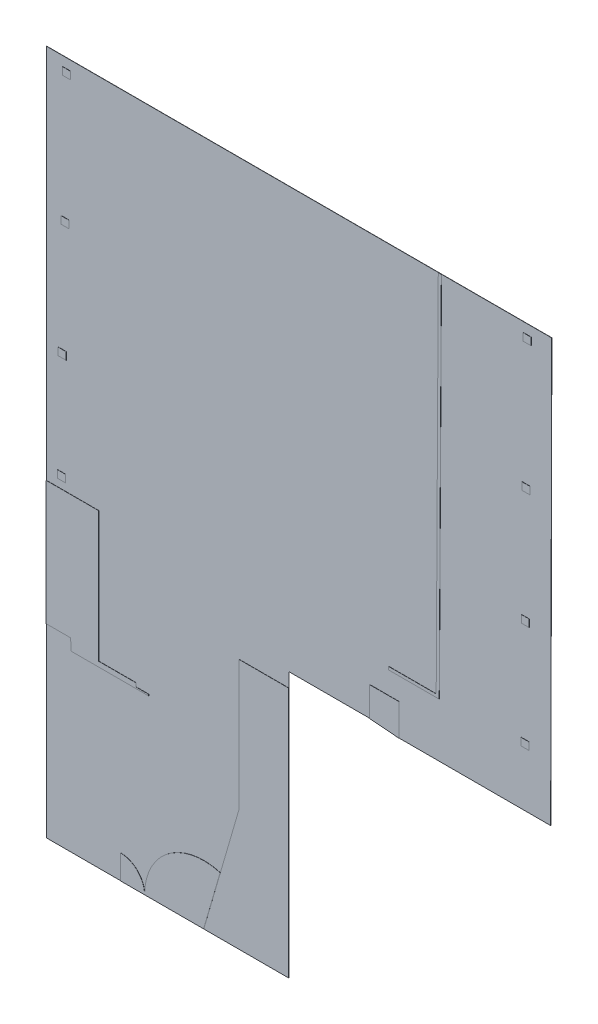
SolidWorks part; units mm, degrees
ref_plane "Alzado" through (0, 0, 0) normal (0, 0, 1) x (1, 0, 0)
ref_plane "Planta" through (0, 0, 0) normal (0, 1, 0) x (1, 0, 0)
ref_plane "Vista lateral" through (0, 0, 0) normal (1, 0, 0) x (0, 0, -1)
sketch "Croquis1" plane through (0, 0, 0) normal (0, 0, 1) x (1, 0, 0)
  line L0 (0, 0) -> (25000, 0)
  line L1 (25000, 0) -> (24950, -20920.8041)
  line L7 (12000, -20800.8041) -> (12000, -33920.8041)
  line L8 (12000, -33920.8041) -> (0, -33920.8041)
  line L9 (0, -33920.8041) -> (0, -24740.8041)
  line L10 (0, -24740.8041) -> (1210, -24740.8041)
  line L11 (1210, -24740.8041) -> (1240, -25300)
  line L12 (1240, -25300) -> (5070, -25300)
  line L13 (5070, -25300) -> (5070, -25230)
  line L15 (16000, -20800.8041) -> (16000, -19350.8041)
  line L16 (5070, -25230) -> (4440, -25230)
  line L17 (4440, -25230) -> (4440, -25050)
  line L18 (4440, -25050) -> (2600, -25050)
  line L19 (2600, -25050) -> (2600, -18600)
  line L20 (2600, -18600) -> (0, -18600)
  line L21 (0, -18600) -> (0, 0)
  line L22 (16000, -19350.8041) -> (17450, -19350.8041)
  line L23 (17450, -19350.8041) -> (17450, -20920.8041)
  line L24 (17450, -20920.8041) -> (24950, -20920.8041)
  line L26 (12000, -20800.8041) -> (16000, -20800.8041)
  dimension "D1" = 25000
  dimension "D3" = 13120
  dimension "D4" = 7500
  dimension "D5" = 1450
  dimension "D6" = 1570
  dimension "D7" = 1450
  dimension "D8" = 4000
  dimension "D9" = 12000
  dimension "D10" = 9180
  dimension "D11" = 1210
  dimension "D12" = 560
  dimension "D13" = 3830
  dimension "D14" = 18600
  dimension "D15" = 2600
  dimension "D16" = 6450
  dimension "D17" = 180
  dimension "D18" = 630
  dimension "D19" = 1840
  dimension "D20" = 70
extrude "Saliente-Extruir1" add sketch "Croquis1" along normal blind 10
sketch "Croquis2" plane through (0, 0, 10) normal (0, 0, 1) x (1, 0, 0)
  line L0 (25000, 0) -> (0, 0) construction
  line L1 (800, -470) -> (1193.7, -470)
  line L2 (800, -470) -> (800, -838.3)
  line L3 (800, -838.3) -> (1193.7, -838.3)
  line L4 (1193.7, -470) -> (1193.7, -838.3)
  line L5 (800, -470) -> (1193.7, -838.3) construction
  line L6 (800, -838.3) -> (1193.7, -470) construction
  line L7 (730, -6888.3) -> (1123.7, -6888.3)
  line L8 (730, -6888.3) -> (730, -7256.6)
  line L9 (730, -7256.6) -> (1123.7, -7256.6)
  line L10 (1123.7, -6888.3) -> (1123.7, -7256.6)
  line L11 (730, -6888.3) -> (1123.7, -7256.6) construction
  line L12 (730, -7256.6) -> (1123.7, -6888.3) construction
  line L13 (558.8, -17861.7) -> (952.5, -17861.7)
  line L14 (558.8, -17861.7) -> (558.8, -18230)
  line L15 (558.8, -18230) -> (952.5, -18230)
  line L16 (952.5, -17861.7) -> (952.5, -18230)
  line L17 (558.8, -17861.7) -> (952.5, -18230) construction
  line L18 (558.8, -18230) -> (952.5, -17861.7) construction
  line L19 (596.9, -12593.4) -> (990.6, -12593.4)
  line L20 (596.9, -12593.4) -> (596.9, -12961.7)
  line L21 (596.9, -12961.7) -> (990.6, -12961.7)
  line L22 (990.6, -12593.4) -> (990.6, -12961.7)
  line L23 (596.9, -12593.4) -> (990.6, -12961.7) construction
  line L24 (596.9, -12961.7) -> (990.6, -12593.4) construction
  line L25 (0, 0) -> (0, -18600) construction
  line L26 (19446.3655, -18250.8041) -> (16946.3655, -18250.8041)
  line L27 (19550, 0) -> (19446.3655, -18250.8041)
  line L28 (19399.9976, 0) -> (19297.2148, -18100.8041)
  line L29 (16946.3655, -18250.8041) -> (16946.3655, -18100.8041)
  line L30 (24950, -20920.8041) -> (25000, 0) construction
  line L31 (16946.3655, -18100.8041) -> (19297.2148, -18100.8041)
  line L32 (19399.9976, 0) -> (19550, 0)
  line L33 (16000, -20800.8041) -> (17450, -20920.8041)
  line L34 (17450, -20920.8041) -> (17450, -19350.8041)
  line L35 (17450, -19350.8041) -> (16000, -19350.8041)
  line L36 (16000, -19350.8041) -> (16000, -20800.8041)
  line L37 (12000, -21500.8041) -> (9550, -21500.8041)
  line L38 (12000, -33920.8041) -> (12000, -20800.8041) construction
  line L39 (9550, -21500.8041) -> (9550, -27900.8041)
  line L41 (12000, -27900.8041) -> (12000, -21500.8041)
  line L43 (3670, -33920.8041) -> (3670, -32720.8041)
  line L44 (9550, -27900.8041) -> (7800, -33920.8041)
  line L46 (12000, -20800.8041) -> (16000, -20800.8041) construction
  line L47 (12000, -33920.8041) -> (12000, -27900.8041)
  line L48 (0, -33920.8041) -> (12000, -33920.8041) construction
  line L49 (7800, -33920.8041) -> (12000, -33920.8041)
  line L50 (9550, -27900.8041) -> (12000, -27900.8041) construction
  line L51 (0, -18600) -> (0, -24740.8041)
  line L52 (0, -24740.8041) -> (1210, -24740.8041)
  line L53 (1210, -24740.8041) -> (1240, -25300)
  line L54 (1240, -25300) -> (5070, -25300)
  line L55 (5070, -25300) -> (5070, -25230)
  line L56 (5070, -25230) -> (4440, -25230)
  line L57 (4440, -25230) -> (4440, -25050)
  line L58 (4440, -25050) -> (2600, -25050)
  line L59 (2600, -25050) -> (2600, -18600)
  line L60 (2600, -18600) -> (0, -18600)
  line L62 (23596.3, -470) -> (23990, -470)
  line L63 (23596.3, -470) -> (23596.3, -838.3)
  line L64 (23596.3, -838.3) -> (23990, -838.3)
  line L65 (23990, -470) -> (23990, -838.3)
  line L66 (23596.3, -470) -> (23990, -838.3) construction
  line L67 (23596.3, -838.3) -> (23990, -470) construction
  line L68 (23932.654, -6888.3) -> (23538.954, -6888.3)
  line L69 (23932.654, -6888.3) -> (23932.654, -7256.6)
  line L70 (23932.654, -7256.6) -> (23538.954, -7256.6)
  line L71 (23538.954, -6888.3) -> (23538.954, -7256.6)
  line L72 (23932.654, -6888.3) -> (23538.954, -7256.6) construction
  line L73 (23932.654, -7256.6) -> (23538.954, -6888.3) construction
  line L74 (23899.0189, -12593.4) -> (23505.3189, -12593.4)
  line L75 (23899.0189, -12593.4) -> (23899.0189, -12961.7)
  line L76 (23899.0189, -12961.7) -> (23505.3189, -12961.7)
  line L77 (23505.3189, -12593.4) -> (23505.3189, -12961.7)
  line L78 (23899.0189, -12593.4) -> (23505.3189, -12961.7) construction
  line L79 (23899.0189, -12961.7) -> (23505.3189, -12593.4) construction
  line L80 (23886.4279, -17861.7) -> (23492.7279, -17861.7)
  line L81 (23886.4279, -17861.7) -> (23886.4279, -18230)
  line L82 (23886.4279, -18230) -> (23492.7279, -18230)
  line L83 (23492.7279, -17861.7) -> (23492.7279, -18230)
  line L84 (23886.4279, -17861.7) -> (23492.7279, -18230) construction
  line L85 (23886.4279, -18230) -> (23492.7279, -17861.7) construction
  line L86 (3670, -33920.8041) -> (4870, -33920.8041)
  arc A1 (4870, -33920.8041) -> (3670, -32720.8041) centre (3670, -33920.8041) ccw
  point P0 (996.85, -654.15)
  point P5 (926.85, -7072.45)
  point P10 (755.65, -18045.85)
  point P15 (793.75, -12777.55)
  point P74 (23793.15, -654.15)
  point P79 (23735.804, -7072.45)
  point P84 (23702.1689, -12777.55)
  point P89 (23689.5779, -18045.85)
  dimension "D39" = 2930
  dimension "D41" = 2400
  dimension "D1" = 393.7
  dimension "D2" = 368.3
  dimension "D3" = 393.7
  dimension "D4" = 393.7
  dimension "D5" = 393.7
  dimension "D6" = 368.3
  dimension "D7" = 368.3
  dimension "D8" = 368.3
  dimension "D9" = 470
  dimension "D10" = 800
  dimension "D11" = 6050
  dimension "D12" = 730
  dimension "D13" = 4900
  dimension "D14" = 596.9
  dimension "D15" = 558.8
  dimension "D16" = 370
  dimension "D17" = 150
  dimension "D18" = 5450
  dimension "D19" = 5510
  dimension "D20" = 150
  dimension "D21" = 2500
  dimension "D22" = 1100
  dimension "D23" = 4200
  dimension "D24" = 700
  dimension "D25" = 2450
  dimension "D26" = 6400
  dimension "D27" = 393.7
  dimension "D28" = 393.7
  dimension "D29" = 393.7
  dimension "D30" = 393.7
  dimension "D31" = 368.3
  dimension "D32" = 368.3
  dimension "D33" = 368.3
  dimension "D34" = 368.3
  dimension "D35" = 1010
  dimension "D36" = 1050
  dimension "D37" = 1070
  dimension "D38" = 1070
extrude "Saliente-Extruir2" add sketch "Croquis2" along normal blind 10
sketch "Croquis3" plane through (0, 0, 10) normal (0, 0, 1) x (1, 0, 0)
  line L0 (7800, -33920.8041) -> (4869.8757, -33920.8041)
  line L1 (7800, -33920.8041) -> (8617.9218, -31107.1531)
  line L2 (9550, -27900.8041) -> (7800, -33920.8041) construction
  line L3 (3670, -33920.8041) -> (4870, -33920.8041) construction
  arc A0 (8617.9218, -31107.1531) -> (4869.8757, -33920.8041) centre (7800, -33920.8041) ccw
  point P1 (4868.333, -33920.8041)
  point P8 (4869.8757, -33920.8041)
extrude "Saliente-Extruir7" add sketch "Croquis3" along normal blind 10
sketch "Croquis4" plane through (0, 0, 20) normal (0, 0, 1) x (1, 0, 0)
  line L2 (8617.9218, -31107.1531) -> (7799.4315, -33922.7598)
extrude "Extruir-Lámina5" add sketch "Croquis4" along normal blind 1 thin
